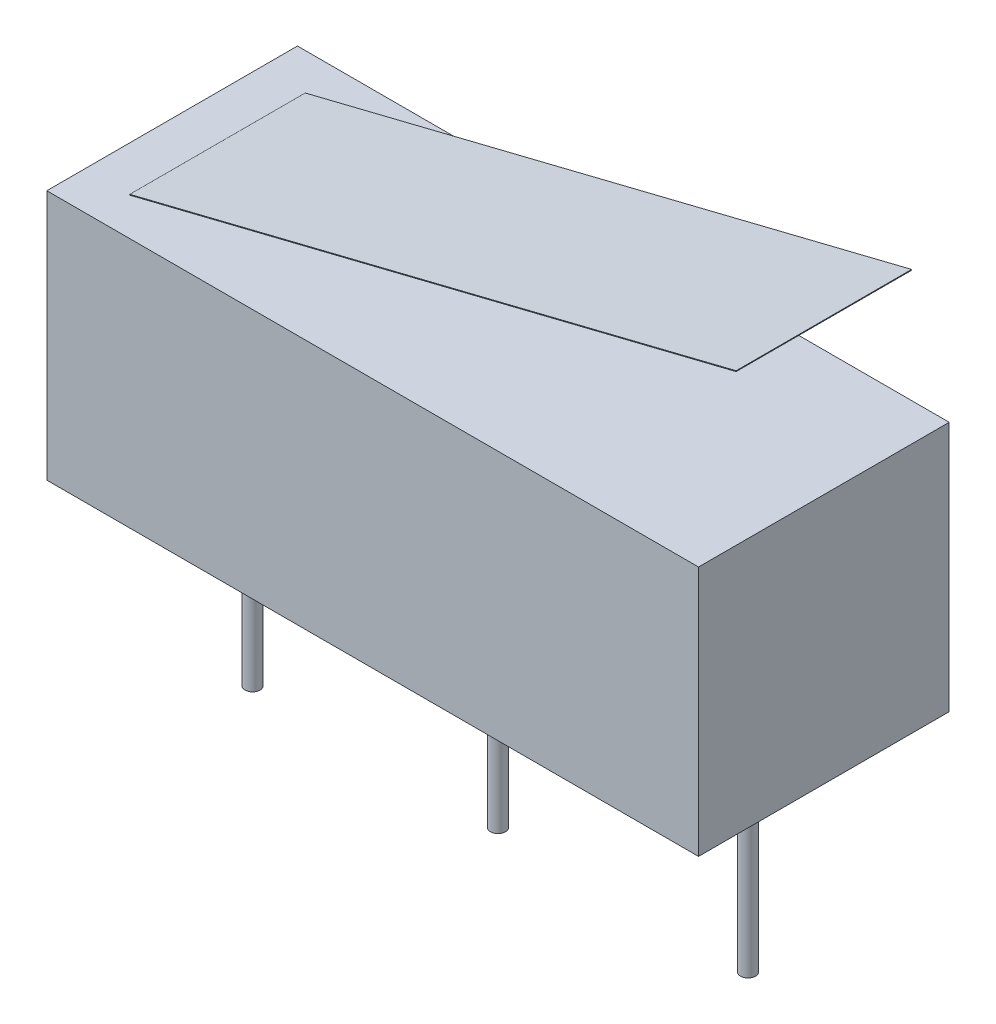
SolidWorks part; units mm, degrees
ref_plane "Alzado" through (0, 0, 0) normal (0, 0, 1) x (1, 0, 0)
ref_plane "Planta" through (0, 0, 0) normal (0, 1, 0) x (1, 0, 0)
ref_plane "Vista lateral" through (0, 0, 0) normal (1, 0, 0) x (0, 0, -1)
sketch "Croquis1" plane through (0, 0, 0) normal (0, 1, 0) x (1, 0, 0)
  line L1 (-6.5, 2.5) -> (6.5, 2.5)
  line L2 (-6.5, 2.5) -> (-6.5, -2.5)
  line L3 (-6.5, -2.5) -> (6.5, -2.5)
  line L4 (6.5, 2.5) -> (6.5, -2.5)
  line L5 (-6.5, 2.5) -> (6.5, -2.5) construction
  line L6 (-6.5, -2.5) -> (6.5, 2.5) construction
  point P0 (0, 0)
  dimension "D1" = 13
  dimension "D2" = 5
extrude "Saliente-Extruir1" add sketch "Croquis1" along normal blind 5 from offset 1
sketch "Croquis2" plane through (0, 1, 0) normal (0, -1, 0) x (1, 0, 0)
  line L0 (-6.5, 0) -> (6.5, 0) construction
  line L1 (-6.5, -2.5) -> (-6.5, 2.5) construction
  line L2 (6.5, 2.5) -> (6.5, -2.5) construction
  circle A0 centre (0, 0) radius 0.15
  circle A1 centre (-4.8965, 0) radius 0.15
  circle A2 centre (4.988, 0) radius 0.15
  dimension "D1" = 0.3
  dimension "D2" = 0.3
  dimension "D3" = 0.3
extrude "Saliente-Extruir2" add sketch "Croquis2" along normal blind 4
sketch "Croquis3" plane through (0, 0, 2.5) normal (0, 0, 1) x (1, 0, 0)
  line L0 (6.5, 6) -> (6.5, 9) construction
  line L1 (-5.5962, 6) -> (6.5, 9)
  line L2 (-6.5, 6) -> (6.5, 6) construction
  line L3 (6.5, 9) -> (6.5, 9.0155)
  line L4 (6.5, 9.0155) -> (-5.5962, 6.0155)
  line L5 (-5.5962, 6.0155) -> (-5.5962, 6)
extrude "Saliente-Extruir3" add sketch "Croquis3" against normal blind 3.5 from offset 0.75 separate body
